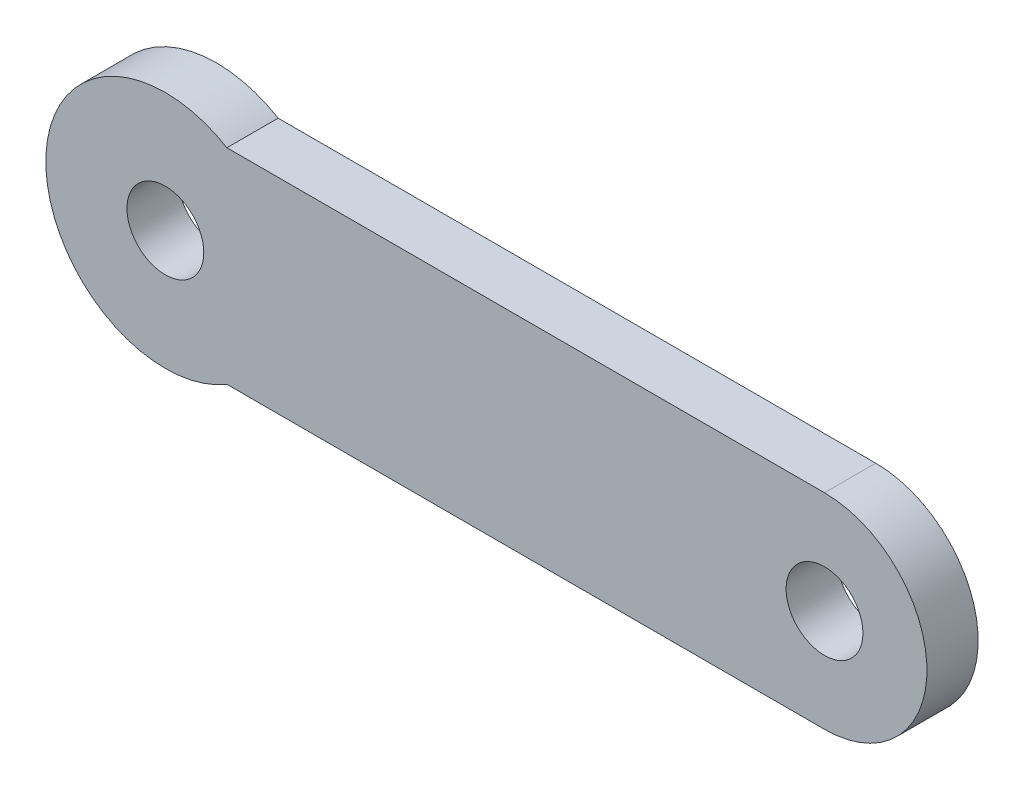
SolidWorks part; units mm, degrees
ref_plane "Front Plane" through (0, 0, 0) normal (0, 0, 1) x (1, 0, 0)
ref_plane "Top Plane" through (0, 0, 0) normal (0, 1, 0) x (1, 0, 0)
ref_plane "Right Plane" through (0, 0, 0) normal (1, 0, 0) x (0, 0, -1)
sketch "Sketch1" plane through (0, 0, 0) normal (0, 0, 1) x (1, 0, 0)
  line L0 (3.6056, 6) -> (38.6056, 6)
  line L1 (3.6056, -6) -> (38.6056, -6)
  arc A0 (3.6056, 6) -> (3.6056, -6) centre (0, 0) ccw
  circle A1 centre (0, 0) radius 2.25
  arc A2 (38.6056, 6) -> (38.6056, -6) centre (38.6056, 0) cw
  circle A3 centre (38.6056, 0) radius 2.25
  dimension "D1" = 4.5
  dimension "D2" = 7
  dimension "D3" = 4.5
  dimension "D4" = 12
  dimension "D5" = 35
extrude "Boss-Extrude1" add sketch "Sketch1" along normal blind 3
